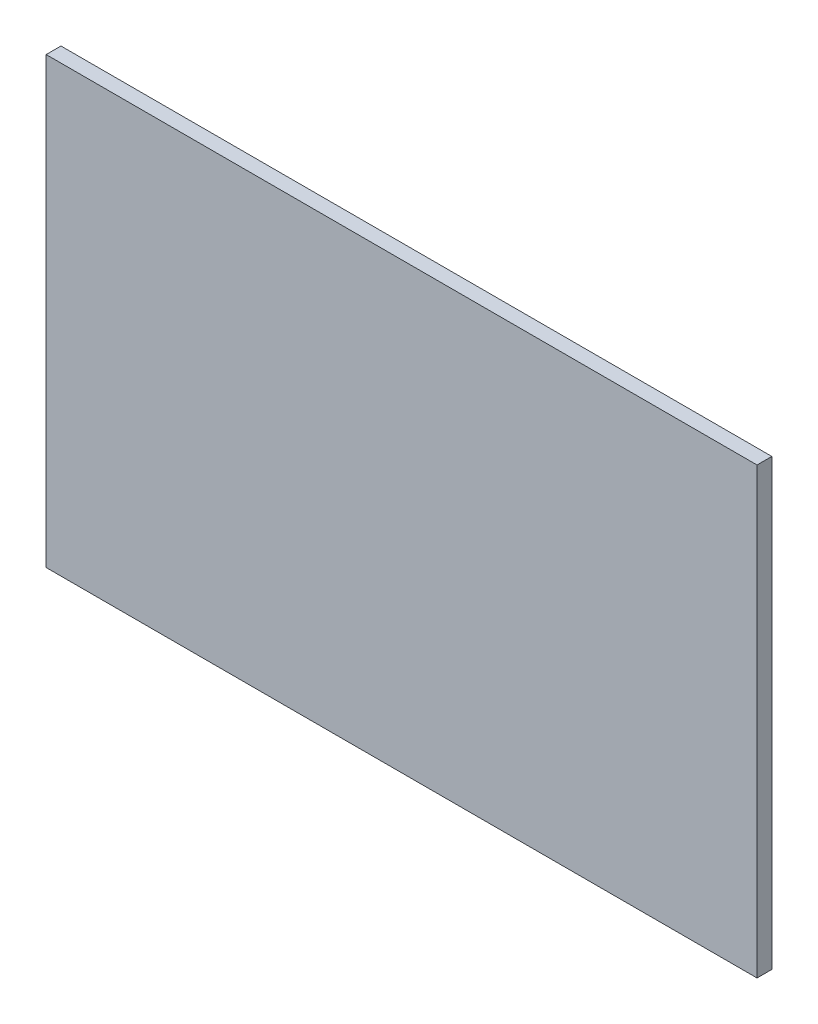
SolidWorks part; units mm, degrees
ref_plane "Front" through (0, 0, 0) normal (0, 0, 1) x (1, 0, 0)
ref_plane "Top" through (0, 0, 0) normal (0, 1, 0) x (1, 0, 0)
ref_plane "Right" through (0, 0, 0) normal (1, 0, 0) x (0, 0, -1)
sketch "Sketch1" plane through (0, 0, 0) normal (0, 0, 1) x (1, 0, 0)
  line L1 (-120, 75) -> (120, 75)
  line L2 (-120, 75) -> (-120, -75)
  line L3 (-120, -75) -> (120, -75)
  line L4 (120, 75) -> (120, -75)
  line L5 (-120, 75) -> (120, -75) construction
  line L6 (-120, -75) -> (120, 75) construction
  point P0 (0, 0)
  dimension "D1" = 240
  dimension "D2" = 150
extrude "Boss-Extrude1" add sketch "Sketch1" along normal blind 5
